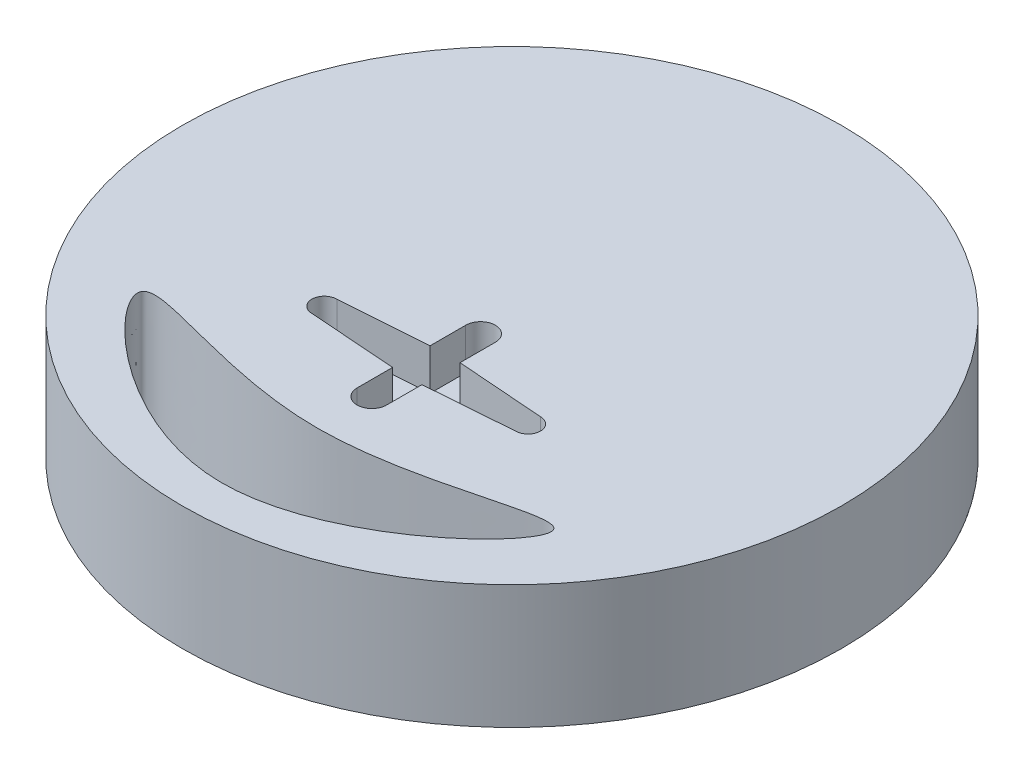
SolidWorks part; units mm, degrees
ref_plane "Front Plane" through (0, 0, 0) normal (0, 0, 1) x (1, 0, 0)
ref_plane "Top Plane" through (0, 0, 0) normal (0, 1, 0) x (1, 0, 0)
ref_plane "Right Plane" through (0, 0, 0) normal (1, 0, 0) x (0, 0, -1)
sketch "Sketch1" plane through (0, 0, 0) normal (0, 1, 0) x (1, 0, 0)
  circle A0 centre (0, 0) radius 50.8
extrude "Boss-Extrude1" add sketch "Sketch1" along normal blind 19.05
sketch "Sketch2" plane through (0, 19.05, 0) normal (0, 1, 0) x (1, 0, 0)
  line L0 (0, 10.8607) -> (0, -26.0542) construction
  line L1 (-15.6972, -13.2075) -> (15.6972, -13.2075) construction
  line L2 (-15.6972, -11.2903) -> (-2.2819, -10.3199)
  line L3 (2.2819, -10.2735) -> (15.6972, -11.2903)
  line L4 (-15.6972, -15.1247) -> (-2.2819, -16.0951)
  line L5 (2.2819, -16.1415) -> (15.6972, -15.1247)
  line L6 (-2.2819, -16.0951) -> (-2.2819, -21.5844)
  line L7 (-2.2819, -4.8306) -> (-2.2819, -10.3199)
  line L8 (2.2819, -4.8306) -> (2.2819, -10.2735)
  line L9 (2.2819, -16.1415) -> (2.2819, -21.5844)
  line L10 (0, -4.8306) -> (0, -21.5844) construction
  arc A1 (-15.6972, -11.2903) -> (-15.6972, -15.1247) centre (-15.6972, -13.2075) ccw
  arc A2 (15.6972, -15.1247) -> (15.6972, -11.2903) centre (15.6972, -13.2075) ccw
  circle A3 centre (0, 0) radius 50.8 construction
  arc A4 (2.2819, -4.8306) -> (-2.2819, -4.8306) centre (0, -4.8306) ccw
  arc A5 (-2.2819, -21.5844) -> (2.2819, -21.5844) centre (0, -21.5844) ccw
  point P3 (0, -13.2075)
  dimension "D1" = 15.6972
extrude "Cut-Extrude1" cut sketch "Sketch2" against normal blind 6.35
sketch "Sketch3" plane through (0, 19.05, 0) normal (0, 1, 0) x (1, 0, 0)
  line L0 (0, 12.8335) -> (0, -72.8433) construction
  spline S0 degree 3 poles (0, -37.2991) (-47.8547, -14.2596) (0, -61.0011) (47.8547, -14.2596) (0, -37.2991) (-47.8547, -14.2596) (0, -61.0011) knots -0.731633 -0.463265 -0.231633 0 0.268367 0.536735 0.768367 1 1.268367 1.536735 1.768367 only from (-31.75, -25.3233) to (-31.75, -25.3233)
  dimension "D1" = 63.5
  dimension "D2" = 31.75
  dimension "D3" = 0
extrude "Cut-Extrude2" cut sketch "Sketch3" against normal through all
sketch "Sketch4" plane through (0, 0, 0) normal (0, -1, 0) x (1, 0, 0)
  line L0 (-44.4379, -24.6153) -> (-25.3879, -24.6153)
  line L1 (25.3879, -24.6153) -> (44.4379, -24.6153)
  line L2 (0, 0) -> (0, 39.1007) construction
  line L3 (-12.7, 16.92) -> (14.224, 16.92)
  line L4 (-12.7, 16.92) -> (-25.3879, -24.6153)
  line L6 (14.224, 16.92) -> (25.3879, -24.6153)
  circle A0 centre (0, 0) radius 50.8 construction
  arc A1 (-44.4379, -24.6153) -> (44.4379, -24.6153) centre (0, 0) ccw
  point P5 (0, -0.5775)
  dimension "D1" = 19.05
  dimension "D3" = 12.7
  dimension "D2" = 19.05
  dimension "D4" = 14.224
extrude "Boss-Extrude2" add sketch "Sketch4" along normal blind 19.05 draft 25 separate body
sketch "Sketch6" plane through (0, 0, 0) normal (0, 0, 1) x (1, 0, 0)
  circle A0 centre (0, -10.16) radius 7.62
  dimension "D1" = 10.16
  dimension "D2" = 15.24
extrude "Cut-Extrude3" cut sketch "Sketch6" against normal through all both and the other way through all
